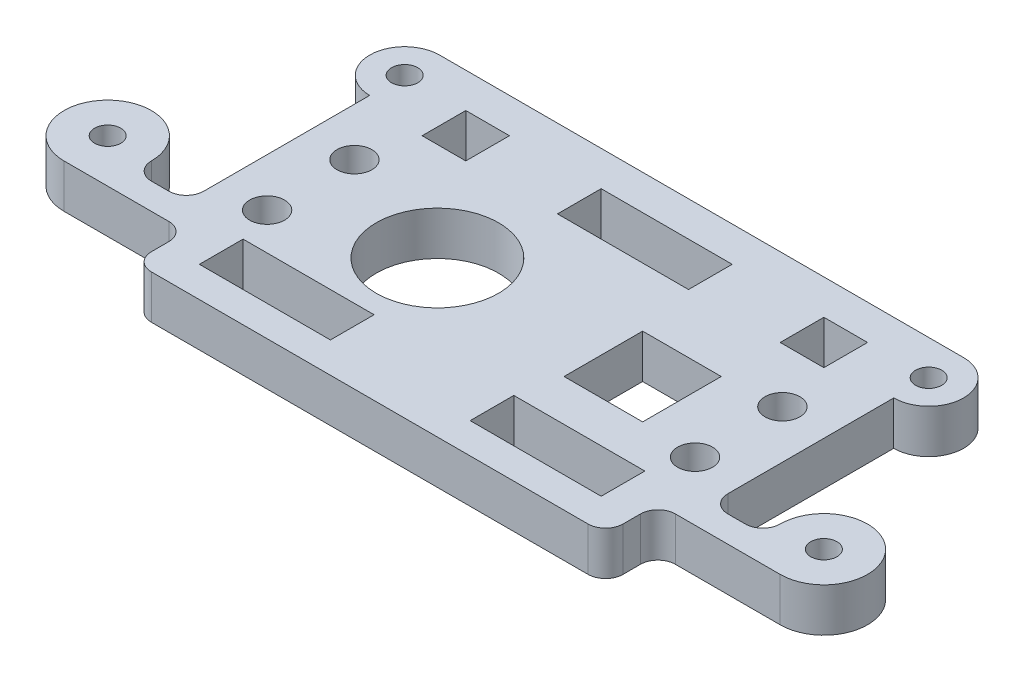
SolidWorks part; units mm, degrees
ref_plane "Front Plane" through (0, 0, 0) normal (0, 0, 1) x (1, 0, 0)
ref_plane "Top Plane" through (0, 0, 0) normal (0, 1, 0) x (1, 0, 0)
ref_plane "Right Plane" through (0, 0, 0) normal (1, 0, 0) x (0, 0, -1)
sketch "Sketch1" plane through (0, 0, 0) normal (0, 1, 0) x (1, 0, 0)
  line L0 (-29, -11.75) -> (-30, -11.75)
  line L2 (-30, -6.75) -> (-30, 12.25)
  line L3 (-30, 20.25) -> (30, 20.25)
  line L4 (30, -6.75) -> (30, 12.25)
  line L5 (0, 20.25) -> (0, -17.75) construction
  line L6 (-30, 0) -> (30, 0) construction
  line L7 (-29, -11.75) -> (-29, -13.75) construction
  line L8 (-23, 16.25) -> (-18, 16.25)
  line L9 (-23, 16.25) -> (-23, 11.25)
  line L10 (-23, 11.25) -> (-18, 11.25)
  line L11 (-18, 16.25) -> (-18, 11.25)
  line L12 (-20.5, 11.25) -> (-20.5, 16.25) construction
  line L13 (-23, 13.75) -> (-18, 13.75) construction
  line L14 (-7.5, 16.25) -> (7.5, 16.25)
  line L15 (-7.5, 16.25) -> (-7.5, 11.25)
  line L16 (-7.5, 11.25) -> (7.5, 11.25)
  line L17 (7.5, 16.25) -> (7.5, 11.25)
  line L18 (0, 11.25) -> (0, 16.25) construction
  line L19 (-7.5, 13.75) -> (7.5, 13.75) construction
  line L20 (18, 16.25) -> (23, 16.25)
  line L21 (18, 16.25) -> (18, 11.25)
  line L22 (18, 11.25) -> (23, 11.25)
  line L23 (23, 16.25) -> (23, 11.25)
  line L24 (20.5, 11.25) -> (20.5, 16.25) construction
  line L25 (18, 13.75) -> (23, 13.75) construction
  line L26 (-23, -9.25) -> (-8, -9.25)
  line L27 (-23, -9.25) -> (-23, -14.25)
  line L28 (-23, -14.25) -> (-8, -14.25)
  line L29 (-8, -9.25) -> (-8, -14.25)
  line L30 (-29, -13.75) -> (-27, -13.75) construction
  line L31 (-25, -17.75) -> (25, -17.75)
  line L32 (8, -9.25) -> (23, -9.25)
  line L33 (8, -9.25) -> (8, -14.25)
  line L34 (8, -14.25) -> (23, -14.25)
  line L35 (23, -9.25) -> (23, -14.25)
  line L37 (29, -11.75) -> (30, -11.75)
  line L38 (-30, -11.75) -> (-41, -11.75)
  line L39 (-27, -13.75) -> (-27, -15.75)
  line L40 (27, -13.75) -> (27, -15.75)
  line L41 (30, -11.75) -> (41, -11.75)
  line L42 (-34, -6.75) -> (-36, -6.75) construction
  line L43 (-34, -6.75) -> (-34, -8.75) construction
  line L44 (32, -8.75) -> (34, -8.75)
  line L45 (-32, -6.75) -> (-32, -8.75) construction
  line L46 (-32, -6.75) -> (-30, -6.75) construction
  line L47 (-34, -8.75) -> (-32, -8.75)
  line L48 (25, -15.75) -> (25, -17.75) construction
  line L49 (25, -15.75) -> (27, -15.75) construction
  line L50 (29, -11.75) -> (29, -13.75) construction
  line L51 (29, -13.75) -> (27, -13.75) construction
  line L52 (-24.5, -5) -> (-24.5, 0) construction
  line L53 (9, 4.5) -> (18, 4.5)
  line L54 (9, 4.5) -> (9, -4.5)
  line L55 (9, -4.5) -> (18, -4.5)
  line L56 (18, 4.5) -> (18, -4.5)
  line L57 (13.5, -4.5) -> (13.5, 4.5) construction
  line L58 (9, 0) -> (18, 0) construction
  line L59 (-24.5, 0) -> (-24.5, 5) construction
  line L60 (30, 0) -> (24.5, 0) construction
  line L61 (24.5, 0) -> (24.5, -5) construction
  line L62 (24.5, 0) -> (24.5, 5) construction
  circle A0 centre (-10, 0) radius 7
  arc A2 (-30, 20.25) -> (-30, 12.25) centre (-30, 16.25) ccw
  arc A3 (30, 12.25) -> (30, 20.25) centre (30, 16.25) ccw
  circle A4 centre (-30, 16.25) radius 1.5
  circle A5 centre (30, 16.25) radius 1.5
  arc A6 (-27, -13.75) -> (-29, -11.75) centre (-29, -13.75) ccw
  arc A7 (29, -11.75) -> (27, -13.75) centre (29, -13.75) ccw
  arc A8 (25, -17.75) -> (27, -15.75) centre (25, -15.75) ccw
  arc A9 (34, -8.75) -> (36, -6.75) centre (34, -6.75) ccw
  arc A10 (-36, -6.75) -> (-34, -8.75) centre (-34, -6.75) ccw
  arc A11 (-32, -8.75) -> (-30, -6.75) centre (-32, -6.75) ccw
  arc A12 (-27, -15.75) -> (-25, -17.75) centre (-25, -15.75) ccw
  arc A13 (30, -6.75) -> (32, -8.75) centre (32, -6.75) ccw
  circle A14 centre (41, -6.75) radius 1.5
  arc A15 (41, -11.75) -> (36, -6.75) centre (41, -6.75) ccw
  arc A16 (-36, -6.75) -> (-41, -11.75) centre (-41, -6.75) ccw
  circle A17 centre (-41, -6.75) radius 1.5
  circle A18 centre (-24.5, -5) radius 2
  circle A19 centre (24.5, -5) radius 2
  circle A21 centre (-24.5, 5) radius 2
  circle A22 centre (24.5, 5) radius 2
  point P59 (22.0476, -5)
  point P77 (25, 5)
  point P84 (0, 13.75)
  point P85 (20.5, 13.75)
  point P86 (25, -5)
  point P91 (-24.1902, 5)
  point P96 (30, 0)
  point P104 (0, 0)
  point P112 (-20.5, 13.75)
  point P159 (13.5, 0)
  dimension "D3" = 14
  dimension "D8" = 8
  dimension "D9" = 8
  dimension "D10" = 3
  dimension "D11" = 3
  dimension "D12" = 5
  dimension "D28" = 4
  dimension "D29" = 2
  dimension "D30" = 2
  dimension "D31" = 4
  dimension "D32" = 2
  dimension "D33" = 2
  dimension "D34" = 4
  dimension "D35" = 4
  dimension "D38" = 11
  dimension "D40" = 3
  dimension "D41" = 10
  dimension "D42" = 3.5
  dimension "D47" = 38
  dimension "D52" = 3
  dimension "D53" = 10
  dimension "D54" = 41
  dimension "D55" = 2
  dimension "D57" = 4
  dimension "D58" = 4
  dimension "D59" = 9
  dimension "D60" = 4
  dimension "D61" = 4
  dimension "D62" = 9
  dimension "D5" = 10
  dimension "D7" = 8
  dimension "D13" = 16.25
  dimension "D14" = 15
  dimension "D15" = 5
  dimension "D16" = 5
  dimension "D17" = 4
  dimension "D18" = 4
  dimension "D19" = 4
  dimension "D20" = 7
  dimension "D21" = 7
  dimension "D22" = 5
  dimension "D23" = 15
  dimension "D24" = 5
  dimension "D25" = 15
  dimension "D26" = 7
  dimension "D27" = 7
  dimension "D36" = 1
  dimension "D37" = 1
  dimension "D39" = 2
  dimension "D43" = 2
  dimension "D44" = 41
  dimension "D45" = 6.75
  dimension "D46" = 3.5
  dimension "D48" = 2
  dimension "D49" = 9.25
  dimension "D50" = 4
  dimension "D51" = 11
  dimension "D56" = 11.25
  dimension "D63" = 5
  dimension "D64" = 5
  dimension "D65" = 5.5
  dimension "D66" = 5.5
  dimension "D67" = 5
  dimension "D68" = 5
extrude "Boss-Extrude1" add sketch "Sketch1" along normal blind 5
